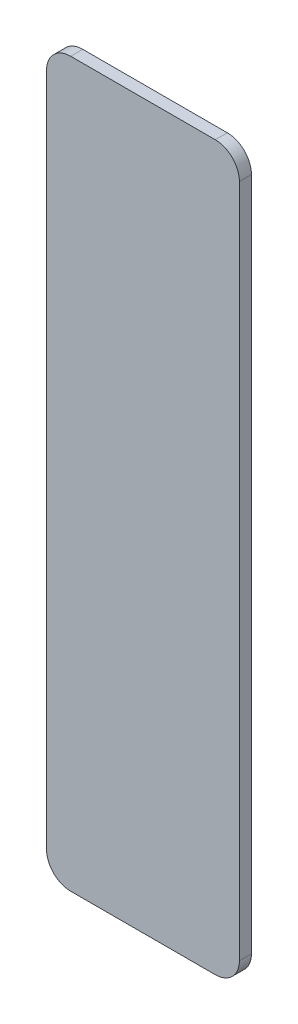
SolidWorks part; units mm, degrees
ref_plane "Front Plane" through (0, 0, 0) normal (0, 0, 1) x (1, 0, 0)
ref_plane "Top Plane" through (0, 0, 0) normal (0, 1, 0) x (1, 0, 0)
ref_plane "Right Plane" through (0, 0, 0) normal (1, 0, 0) x (0, 0, -1)
sketch "Sketch1" plane through (0, 0, 0) normal (0, 0, 1) x (1, 0, 0)
  line L1 (-4, -15) -> (4, -15)
  line L2 (-4, -15) -> (-4, 15)
  line L3 (-4, 15) -> (4, 15)
  line L4 (4, -15) -> (4, 15)
  line L5 (-4, -15) -> (4, 15) construction
  line L6 (-4, 15) -> (4, -15) construction
  point P0 (0, 0)
  dimension "D1" = 8
  dimension "D2" = 30
extrude "Boss-Extrude1" add sketch "Sketch1" along normal blind 0.5
fillet "Fillet1" radius 1 4 edges at (-4, -15, 0.25) (4, -15, 0.25) (4, 15, 0.25) (-4, 15, 0.25)
